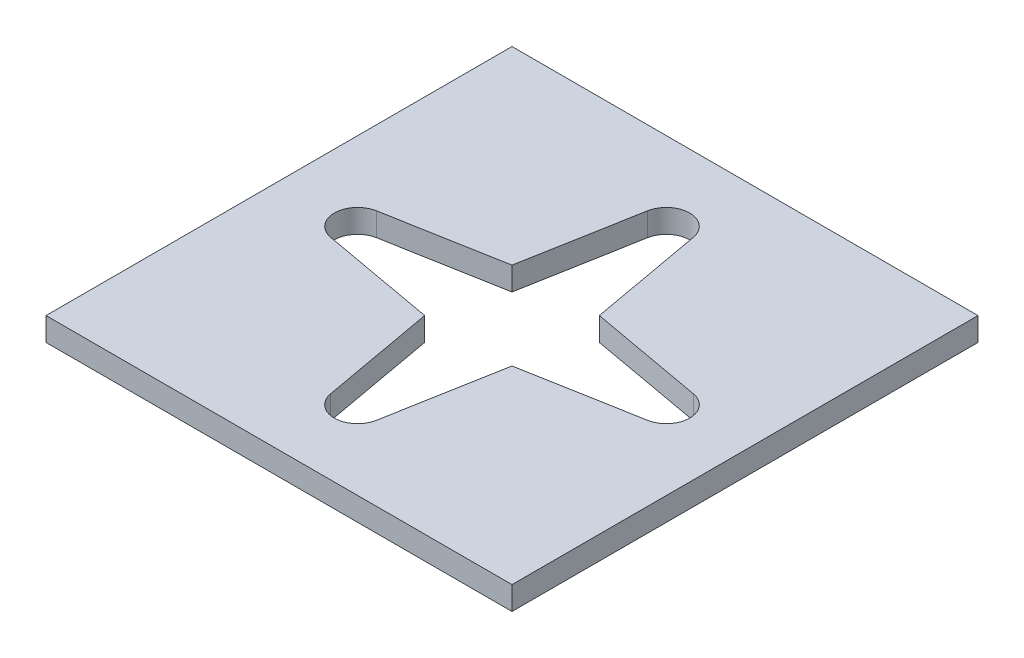
SolidWorks part; units mm, degrees
ref_plane "Front Plane" through (0, 0, 0) normal (0, 0, 1) x (1, 0, 0)
ref_plane "Top Plane" through (0, 0, 0) normal (0, 1, 0) x (1, 0, 0)
ref_plane "Right Plane" through (0, 0, 0) normal (1, 0, 0) x (0, 0, -1)
sketch "Sketch1" plane through (0, 0, 0) normal (0, 1, 0) x (1, 0, 0)
  line L1 (-25.4, 25.4) -> (25.4, 25.4)
  line L2 (-25.4, 25.4) -> (-25.4, -25.4)
  line L3 (-25.4, -25.4) -> (25.4, -25.4)
  line L4 (25.4, 25.4) -> (25.4, -25.4)
  line L5 (-25.4, 25.4) -> (25.4, -25.4) construction
  line L6 (-25.4, -25.4) -> (25.4, 25.4) construction
  point P0 (0, 0)
  dimension "D1" = 50.8
  dimension "D2" = 50.8
extrude "Boss-Extrude1" add sketch "Sketch1" along normal blind 2.54
sketch "Sketch2" plane through (0, 0, 0) normal (0, -1, 0) x (1, 0, 0)
  line L0 (-40.1611, 0) -> (40.1611, 0) construction
  line L1 (0, 28.3552) -> (0, -28.3552) construction
  line L2 (0, 0) -> (-4.7595, 4.7595) construction
  line L3 (-4.7595, 4.7595) -> (-2.4996, 17.2787)
  line L4 (-4.7595, 4.7595) -> (-17.2787, 2.4996)
  line L5 (4.7595, 4.7595) -> (17.2787, 2.4996)
  line L6 (4.7595, 4.7595) -> (2.4996, 17.2787)
  line L7 (4.7595, -4.7595) -> (17.2787, -2.4996)
  line L8 (4.7595, -4.7595) -> (2.4996, -17.2787)
  line L9 (-4.7595, -4.7595) -> (-2.4996, -17.2787)
  line L10 (-4.7595, -4.7595) -> (-17.2787, -2.4996)
  circle A0 centre (0, 0) radius 19.3675 construction
  arc A1 (2.4996, 17.2787) -> (-2.4996, 17.2787) centre (0, 16.8275) ccw
  arc A2 (-17.2787, 2.4996) -> (-17.2787, -2.4996) centre (-16.8275, 0) ccw
  arc A4 (17.2787, 2.4996) -> (17.2787, -2.4996) centre (16.8275, 0) cw
  arc A5 (2.4996, -17.2787) -> (-2.4996, -17.2787) centre (0, -16.8275) cw
  point P6 (0, 0)
  point P9 (0, 0)
  dimension "D1" = 38.735
  dimension "D2" = 5.08
  dimension "D4" = 5.08
  dimension "D5" = 16.8275
  dimension "D7" = 16.8275
extrude "Cut-Extrude1" cut sketch "Sketch2" against normal through all contours L3 A1 L6 L5 A4 L7 L8 A5 L9 L10 A2 L4
